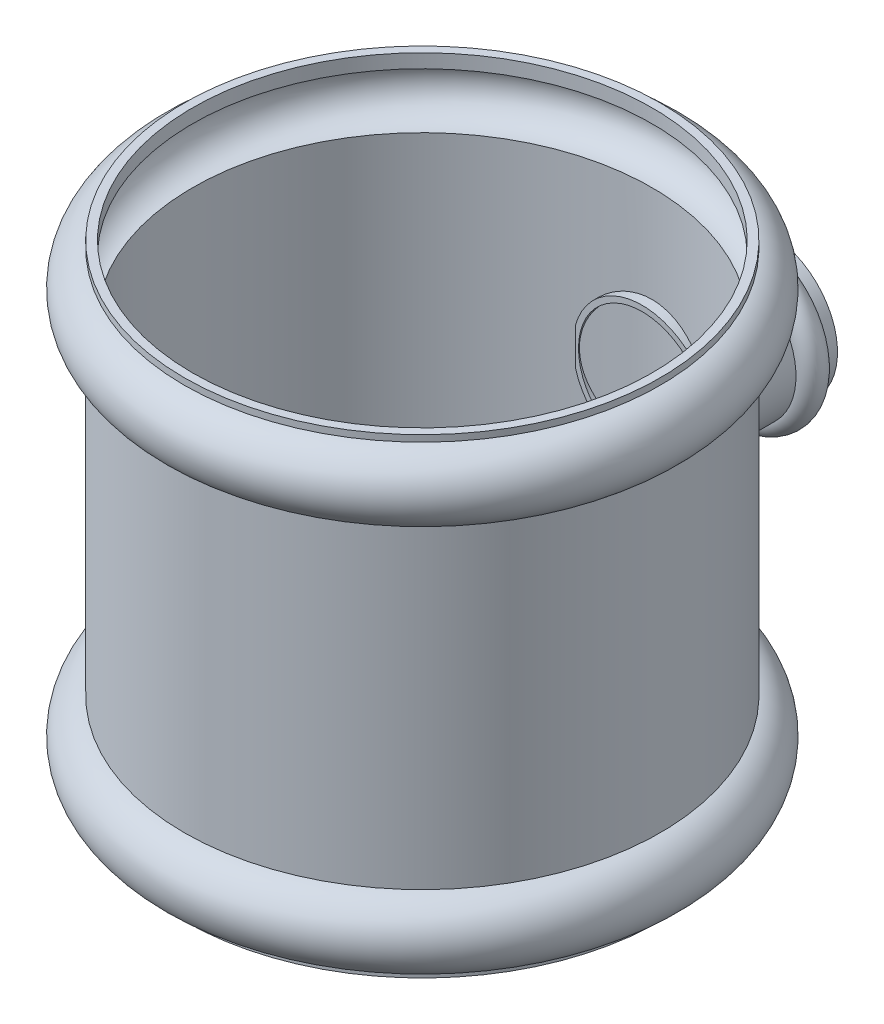
SolidWorks part; units mm, degrees
ref_plane "Спереди" through (0, 0, 0) normal (0, 0, 1) x (1, 0, 0)
ref_plane "Сверху" through (0, 0, 0) normal (0, 1, 0) x (1, 0, 0)
ref_plane "Справа" through (0, 0, 0) normal (1, 0, 0) x (0, 0, -1)
sketch "Эскиз2" plane through (0, 0, 0) normal (0, 0, 1) x (1, 0, 0)
  line L0 (83, 60) -> (83, -60)
  line L1 (83, 80) -> (83, 85)
  line L2 (83, -80) -> (83, -85)
  line L3 (0, 137.8137) -> (0, -119.9955) construction
  arc A0 (83, 60) -> (83, 80) centre (83, 70) ccw
  arc A1 (83, -60) -> (83, -80) centre (83, -70) cw
revolve "Повернуть-Тонкостенный1" add sketch "Эскиз2" angle 360 about L3 wall 3
sketch "Эскиз3" plane through (0, 0, 0) normal (0, 1, 0) x (1, 0, 0)
  line L0 (25, 110) -> (25, 79.414)
  line L1 (0, 125.3985) -> (0, 59.7564) construction
  line L2 (25, 125) -> (25, 120)
  arc A0 (25, 120) -> (25, 110) centre (25, 115) cw
revolve "Повернуть-Тонкостенный3" add sketch "Эскиз3" angle 360 about L1
